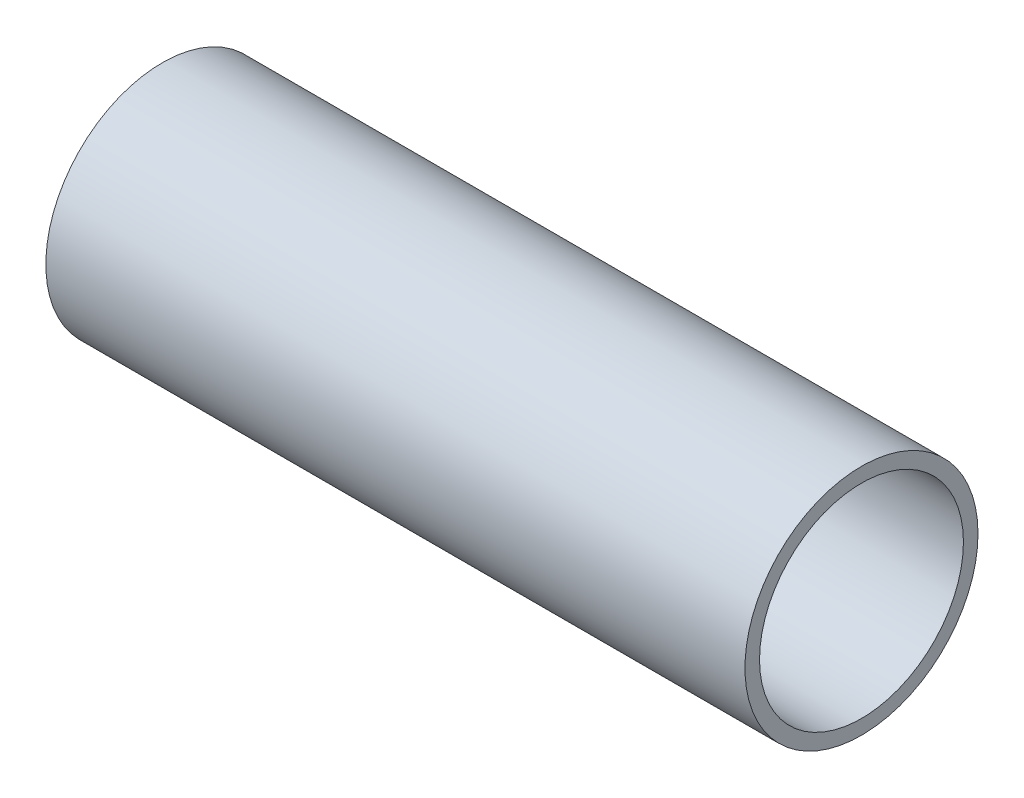
SolidWorks part; units mm, degrees
material "6061-T6 (SS)"
ref_plane "Front Plane" through (0, 0, 0) normal (0, 0, 1) x (1, 0, 0)
ref_plane "Top Plane" through (0, 0, 0) normal (0, 1, 0) x (1, 0, 0)
ref_plane "Right Plane" through (0, 0, 0) normal (1, 0, 0) x (0, 0, -1)
sketch "Sketch3" plane through (0, 0, 0) normal (1, 0, 0) x (0, 0, -1)
  circle A0 centre (0, 0) radius 22.225
  circle A1 centre (0, 0) radius 25.4
  dimension "D1" = 50.8
  dimension "D2" = 44.45
extrude "Boss-Extrude1" add sketch "Sketch3" along normal blind 152.4
